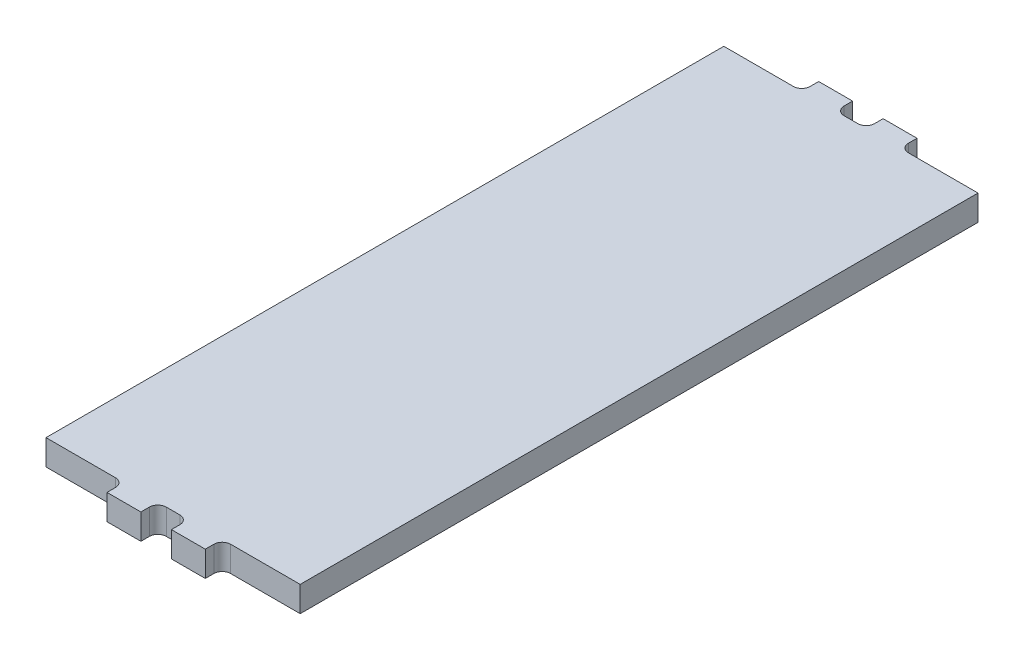
SolidWorks part; units mm, degrees
ref_plane "Спереди" through (0, 0, 0) normal (0, 0, 1) x (1, 0, 0)
ref_plane "Сверху" through (0, 0, 0) normal (0, 1, 0) x (1, 0, 0)
ref_plane "Справа" through (0, 0, 0) normal (1, 0, 0) x (0, 0, -1)
other "Configuration Table"
sketch "Sketch1" plane through (0, 0, 0) normal (0, 1, 0) x (1, 0, 0)
  line L0 (-7.5, -20.2273) -> (-7.5, 19.7727)
  line L1 (7.5, -20.2273) -> (7.5, 19.7727)
  line L2 (-7.5, 19.7727) -> (-3.4, 19.7727)
  line L3 (7.5, -20.2273) -> (3.4, -20.2273)
  line L4 (7.5, 19.7727) -> (-7.5, -19.242) construction
  line L5 (-2.9, 20.7727) -> (-0.9, 20.7727)
  line L6 (2.9, -21.2273) -> (0.9, -21.2273)
  line L9 (2.9, -21.2273) -> (2.9, -20.7273)
  line L10 (-2.9, -21.2273) -> (-2.9, -20.7273)
  line L11 (0.9, -21.2273) -> (0.9, -20.7273)
  line L13 (-0.9, -21.2273) -> (-0.9, -20.7273)
  line L14 (0.9, 20.7727) -> (2.9, 20.7727)
  line L15 (-2.9, -21.2273) -> (-2.9, 25.5802) construction
  line L16 (-0.9, -21.2273) -> (-0.9, 25.5802) construction
  line L17 (3.4, 19.7727) -> (7.5, 19.7727)
  line L18 (0.9, -21.2273) -> (0.9, 25.5802) construction
  line L19 (2.9, -21.2273) -> (2.9, 25.5802) construction
  line L20 (-0.4, 19.7727) -> (0.4, 19.7727)
  line L21 (-0.9, 20.2727) -> (-0.9, 20.7727)
  line L22 (-2.9, 20.2727) -> (-2.9, 20.7727)
  line L23 (0.9, 20.2727) -> (0.9, 20.7727)
  line L24 (2.9, 20.2727) -> (2.9, 20.7727)
  line L25 (-0.9, -21.2273) -> (-2.9, -21.2273)
  line L26 (0.4, -20.2273) -> (-0.4, -20.2273)
  line L27 (-3.4, -20.2273) -> (-7.5, -20.2273)
  arc A0 (3.4, 19.7727) -> (2.9, 20.2727) centre (3.4, 20.2727) cw
  arc A1 (-3.4, 19.7727) -> (-2.9, 20.2727) centre (-3.4, 20.2727) ccw
  arc A2 (2.9, -20.7273) -> (3.4, -20.2273) centre (3.4, -20.7273) cw
  arc A3 (-2.9, -20.7273) -> (-3.4, -20.2273) centre (-3.4, -20.7273) ccw
  arc A4 (0.9, -20.7273) -> (0.4, -20.2273) centre (0.4, -20.7273) ccw
  arc A5 (-0.9, -20.7273) -> (-0.4, -20.2273) centre (-0.4, -20.7273) cw
  arc A6 (0.9, 20.2727) -> (0.4, 19.7727) centre (0.4, 20.2727) cw
  arc A7 (-0.9, 20.2727) -> (-0.4, 19.7727) centre (-0.4, 20.2727) ccw
  point P24 (0, 0)
  point P29 (0, 0)
  point P32 (2.9, 19.7727)
  point P35 (-2.9, 19.7727)
  point P40 (-2.9, -20.2273)
  point P43 (0.9, -20.2273)
  point P46 (-0.9, -20.2273)
  point P49 (0.9, 19.7727)
  point P52 (-0.9, 19.7727)
  dimension "D3" = 0.5
  dimension "D1" = 2
  dimension "D2" = 2
extrude "Boss-Extrude1" add sketch "Sketch1" along normal blind 1.5
sketch "Sketch2" plane through (0, 0, 0) normal (0, -1, 0) x (1, 0, 0)
  line L0 (-0.95, -16.4273) -> (-2.95, -16.4273)
  line L1 (-0.95, -16.4273) -> (-0.95, -17.9273)
  line L2 (-0.95, -17.9273) -> (-2.95, -17.9273)
  line L3 (-2.95, -16.4273) -> (-2.95, -17.9273)
  line L4 (2.95, -16.4273) -> (2.95, -17.9273)
  line L5 (0.95, -17.9273) -> (2.95, -17.9273)
  line L6 (0.95, -16.4273) -> (0.95, -17.9273)
  line L7 (0.95, -16.4273) -> (2.95, -16.4273)
  line L8 (-0.95, -13.4273) -> (-2.95, -13.4273)
  line L9 (-0.95, -13.4273) -> (-0.95, -14.9273)
  line L10 (-0.95, -14.9273) -> (-2.95, -14.9273)
  line L11 (-2.95, -13.4273) -> (-2.95, -14.9273)
  line L12 (2.95, -13.4273) -> (2.95, -14.9273)
  line L13 (0.95, -14.9273) -> (2.95, -14.9273)
  line L14 (0.95, -13.4273) -> (0.95, -14.9273)
  line L15 (0.95, -13.4273) -> (2.95, -13.4273)
  line L16 (-0.95, -10.4273) -> (-2.95, -10.4273)
  line L17 (-0.95, -10.4273) -> (-0.95, -11.9273)
  line L18 (-0.95, -11.9273) -> (-2.95, -11.9273)
  line L19 (-2.95, -10.4273) -> (-2.95, -11.9273)
  line L20 (-0.95, -7.4273) -> (-2.95, -7.4273)
  line L21 (-0.95, -7.4273) -> (-0.95, -8.9273)
  line L22 (-0.95, -8.9273) -> (-2.95, -8.9273)
  line L23 (-2.95, -7.4273) -> (-2.95, -8.9273)
  line L24 (-0.95, -4.4273) -> (-2.95, -4.4273)
  line L25 (-0.95, -4.4273) -> (-0.95, -5.9273)
  line L26 (-0.95, -5.9273) -> (-2.95, -5.9273)
  line L27 (-2.95, -4.4273) -> (-2.95, -5.9273)
  line L28 (-0.95, -1.4273) -> (-2.95, -1.4273)
  line L29 (-0.95, -1.4273) -> (-0.95, -2.9273)
  line L30 (-0.95, -2.9273) -> (-2.95, -2.9273)
  line L31 (-2.95, -1.4273) -> (-2.95, -2.9273)
  line L32 (-0.95, 1.5727) -> (-2.95, 1.5727)
  line L33 (-0.95, 1.5727) -> (-0.95, 0.0727)
  line L34 (-0.95, 0.0727) -> (-2.95, 0.0727)
  line L35 (-2.95, 1.5727) -> (-2.95, 0.0727)
  line L36 (-0.95, 4.5727) -> (-2.95, 4.5727)
  line L37 (-0.95, 4.5727) -> (-0.95, 3.0727)
  line L38 (-0.95, 3.0727) -> (-2.95, 3.0727)
  line L39 (-2.95, 4.5727) -> (-2.95, 3.0727)
  line L40 (-0.95, 7.5727) -> (-2.95, 7.5727)
  line L41 (-0.95, 7.5727) -> (-0.95, 6.0727)
  line L42 (-0.95, 6.0727) -> (-2.95, 6.0727)
  line L43 (-2.95, 7.5727) -> (-2.95, 6.0727)
  line L44 (2.95, 7.5727) -> (2.95, 6.0727)
  line L45 (-0.95, 10.5727) -> (-2.95, 10.5727)
  line L46 (-0.95, 10.5727) -> (-0.95, 9.0727)
  line L47 (-0.95, 9.0727) -> (-2.95, 9.0727)
  line L48 (-2.95, 10.5727) -> (-2.95, 9.0727)
  line L49 (2.95, 10.5727) -> (2.95, 9.0727)
  line L50 (0.95, 9.0727) -> (2.95, 9.0727)
  line L51 (0.95, 10.5727) -> (0.95, 9.0727)
  line L52 (0.95, 10.5727) -> (2.95, 10.5727)
  line L53 (0.95, 6.0727) -> (2.95, 6.0727)
  line L54 (0.95, 7.5727) -> (0.95, 6.0727)
  line L55 (0.95, 7.5727) -> (2.95, 7.5727)
  point P0 (7.5, -19.7727)
extrude "Boss-Extrude2" add sketch "Sketch2" along normal blind 0.01
